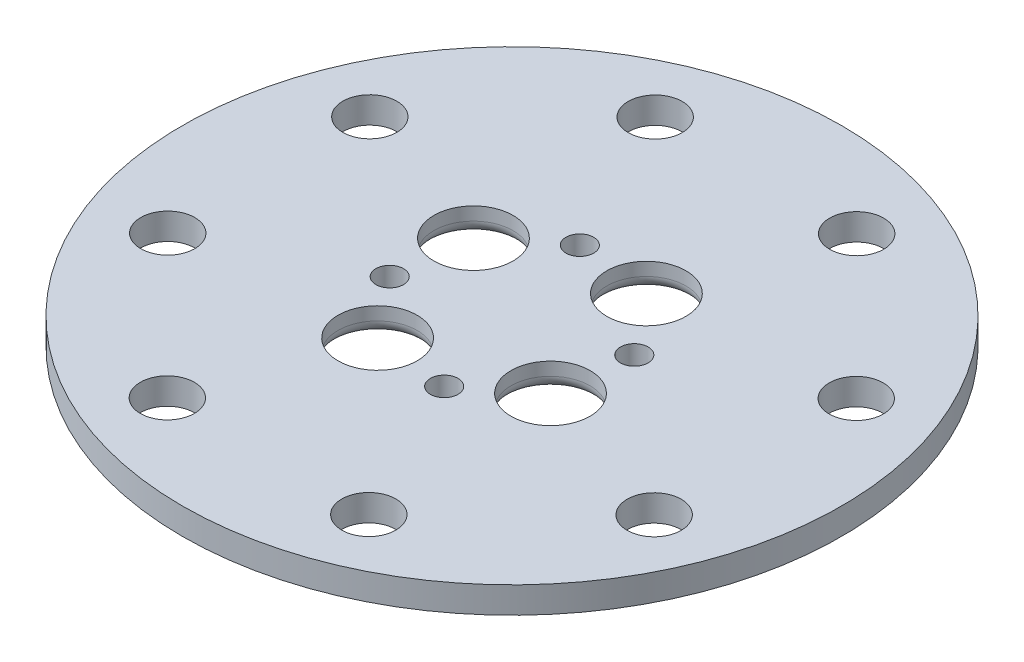
SolidWorks part; units mm, degrees
material "PTFE (general)"
ref_plane "Front Plane" through (0, 0, 0) normal (0, 0, 1) x (1, 0, 0)
ref_plane "Top Plane" through (0, 0, 0) normal (0, 1, 0) x (1, 0, 0)
ref_plane "Right Plane" through (0, 0, 0) normal (1, 0, 0) x (0, 0, -1)
sketch "Sketch1" plane through (0, 0, 0) normal (0, 1, 0) x (1, 0, 0)
  circle A0 centre (0, 0) radius 25
  dimension "D1" = 50
extrude "Boss-Extrude1" add sketch "Sketch1" along normal blind 2
sketch "Sketch2" plane through (0, 2, 0) normal (0, 1, 0) x (1, 0, 0)
  line L0 (0, 0) -> (2.0664, -7.2097) construction
  line L1 (0, 0) -> (-3.6369, -6.5592) construction
  circle A0 centre (0, 0) radius 7.5 construction
  circle A1 centre (-2.0664, 7.2097) radius 1.05
  circle A2 centre (7.2097, 2.0664) radius 1.05
  circle A3 centre (2.0664, -7.2097) radius 1.05
  circle A4 centre (-7.2097, -2.0664) radius 1.05
  circle A9 centre (-3.6369, -6.5592) radius 3
  circle A10 centre (-6.5592, 3.6369) radius 3
  circle A11 centre (3.6369, 6.5592) radius 3
  circle A12 centre (6.5592, -3.6369) radius 3
  point P21 (0, 0)
  point P23 (0, 0)
  dimension "D1" = 15
  dimension "D2" = 2.1
  dimension "D4" = 6
  dimension "D5" = 45
  dimension "D3" = 4
  dimension "D6" = 4
extrude "Cut-Extrude1" cut sketch "Sketch2" against normal through all
sketch "Sketch3" [suppressed] plane through (0, 2, 0) normal (0, 1, 0) x (1, 0, 0)
  circle A0 centre (0, 0) radius 4
  circle A1 centre (0, 0) radius 17.5 construction
  circle A2 centre (17.0562, -3.9161) radius 4
  circle A3 centre (9.2915, -14.8296) radius 4
  circle A4 centre (-3.9161, -17.0562) radius 4
  circle A5 centre (-14.8296, -9.2915) radius 4
  circle A6 centre (-17.0562, 3.9161) radius 4
  circle A7 centre (-9.2915, 14.8296) radius 4
  circle A8 centre (3.9161, 17.0562) radius 4
  circle A9 centre (14.8296, 9.2915) radius 4
  point P23 (0, 0)
  dimension "D1" = 35
  dimension "8" = 8
  dimension "D2" = 8
  dimension "D3" = 8
ref_plane "Plane1" through (0, 0, -25) normal (0, 0, -1) x (-1, 0, 0)
fillet "Fillet1" radius 1 4 edges at (-6.5592, 0, -0.6369) (3.6369, 0, -3.5592) (6.5592, 0, 6.6369) (-3.6369, 0, 9.5592)
sketch "Sketch4" plane through (0, 0, 0) normal (0, -1, 0) x (1, 0, 0)
  circle A0 centre (0, 0) radius 20 construction
  circle A5 centre (-18.4887, 7.6267) radius 2.05
  circle A6 centre (-18.4887, 7.6267) radius 2.05 construction
  circle A7 centre (-7.6806, 18.4664) radius 2.05
  circle A8 centre (7.6267, 18.4887) radius 2.05
  circle A9 centre (18.4664, 7.6806) radius 2.05
  circle A10 centre (18.4887, -7.6267) radius 2.05
  circle A11 centre (7.6806, -18.4664) radius 2.05
  circle A12 centre (-7.6267, -18.4887) radius 2.05
  circle A13 centre (-18.4664, -7.6806) radius 2.05
  point P31 (0, 0)
  dimension "D1" = 40
  dimension "D2" = 0
  dimension "D4" = 4.1
  dimension "D3" = 8
extrude "Cut-Extrude3" cut sketch "Sketch4" against normal through all
sketch "Sketch6" plane through (0, 0, 0) normal (0, -1, 0) x (1, 0, 0)
  circle A0 centre (20.3384, -6.9714) radius 1.55
  circle A1 centre (0, 0) radius 21.5 construction
  dimension "D1" = 3.1
  dimension "D2" = 43
extrude "Cut-Extrude4" [suppressed] cut sketch "Sketch6" against normal through all
